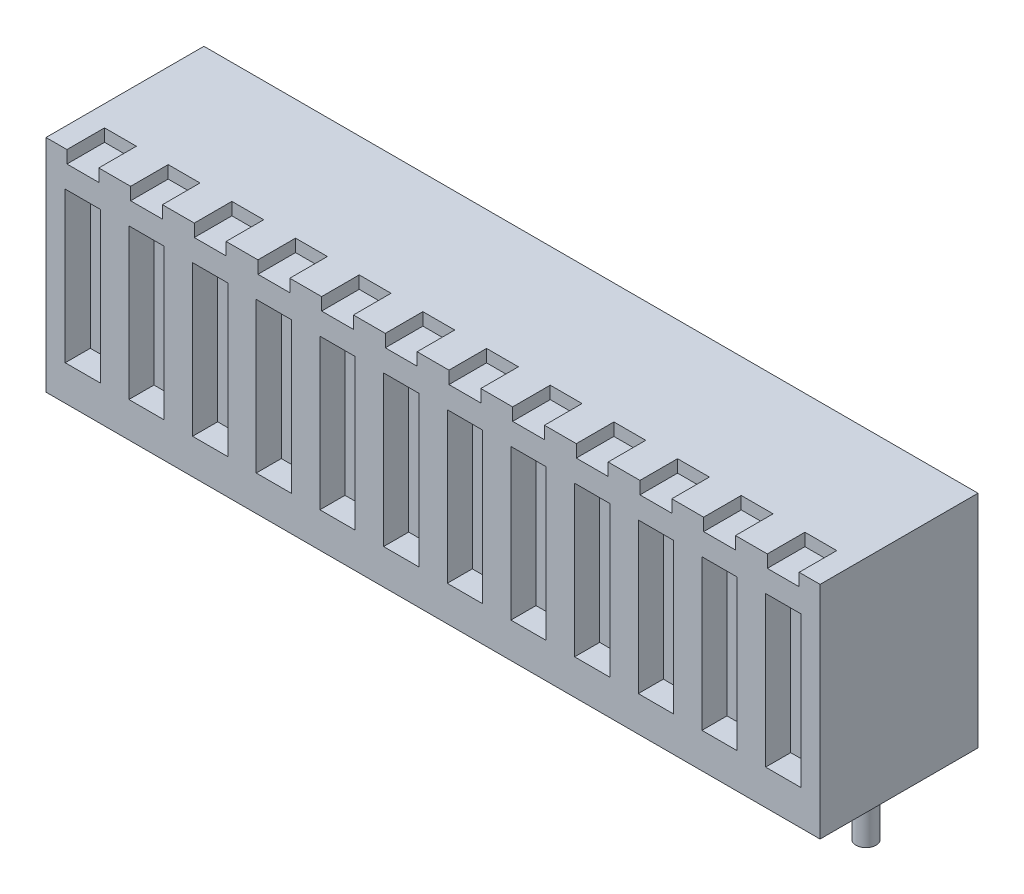
SolidWorks part; units mm, degrees
ref_plane "Front Plane" through (0, 0, 0) normal (0, 0, 1) x (1, 0, 0)
ref_plane "Top Plane" through (0, 0, 0) normal (0, 1, 0) x (1, 0, 0)
ref_plane "Right Plane" through (0, 0, 0) normal (1, 0, 0) x (0, 0, -1)
sketch "Sketch2" plane through (0, 0, 0) normal (0, 1, 0) x (1, 0, 0)
  line L1 (-15.44, -3.15) -> (15.44, -3.15)
  line L2 (-15.44, -3.15) -> (-15.44, 3.15)
  line L3 (-15.44, 3.15) -> (15.44, 3.15)
  line L4 (15.44, -3.15) -> (15.44, 3.15)
  line L5 (-15.44, -3.15) -> (15.44, 3.15) construction
  line L6 (-15.44, 3.15) -> (15.44, -3.15) construction
  point P0 (0, 0)
  dimension "D1" = 30.88
  dimension "D2" = 6.3
extrude "Boss-Extrude1" add sketch "Sketch2" along normal blind 8.8
sketch "Sketch3" plane through (0, 0, 0) normal (0, -1, 0) x (1, 0, 0)
  line L0 (-15.44, -3.15) -> (-15.44, 3.15) construction
  line L1 (15.44, -3.15) -> (-15.44, -3.15) construction
  circle A0 centre (-13.97, -0.15) radius 0.4
  point P4 (-13.97, 0)
  point P5 (0, 0)
  dimension "D2" = 0.8
  dimension "D1" = 1.47
  dimension "D3" = 3
extrude "Boss-Extrude2" add sketch "Sketch3" along normal blind 2.4
sketch "Sketch4" plane through (0, 0, 3.15) normal (0, 0, 1) x (1, 0, 0)
  line L0 (-15.44, 8.8) -> (-15.44, 0) construction
  line L1 (-14.6727, 7.4) -> (-13.2673, 7.4)
  line L2 (-14.6727, 7.4) -> (-14.6727, 1.4)
  line L3 (-14.6727, 1.4) -> (-13.2673, 1.4)
  line L4 (-13.2673, 7.4) -> (-13.2673, 1.4)
  line L5 (-14.6727, 7.4) -> (-13.2673, 1.4) construction
  line L6 (-14.6727, 1.4) -> (-13.2673, 7.4) construction
  point P0 (-13.97, 4.4)
  point P5 (-15.44, 4.4)
  dimension "D1" = 6
  dimension "D2" = 1.4054
  dimension "D3" = 1.47
extrude "Cut-Extrude1" cut sketch "Sketch4" against normal blind 1
sketch "Sketch5" plane through (0, 8.8, 0) normal (0, 1, 0) x (1, 0, 0)
  line L0 (-15.44, -3.15) -> (15.44, -3.15) construction
  line L1 (-14.605, -3.15) -> (-13.335, -3.15)
  line L2 (-14.605, -3.15) -> (-14.605, -1.65)
  line L3 (-14.605, -1.65) -> (-13.335, -1.65)
  line L4 (-13.335, -3.15) -> (-13.335, -1.65)
  point P6 (-13.97, -3.15)
  dimension "D1" = 1.5
  dimension "D2" = 1.27
  dimension "D3" = 1.47
extrude "Cut-Extrude2" cut sketch "Sketch5" against normal blind 0.5
pattern_linear "LPattern1" count 12 spacing 2.54 along (1, 0, 0) of "Boss-Extrude2", "Cut-Extrude1", "Cut-Extrude2"
